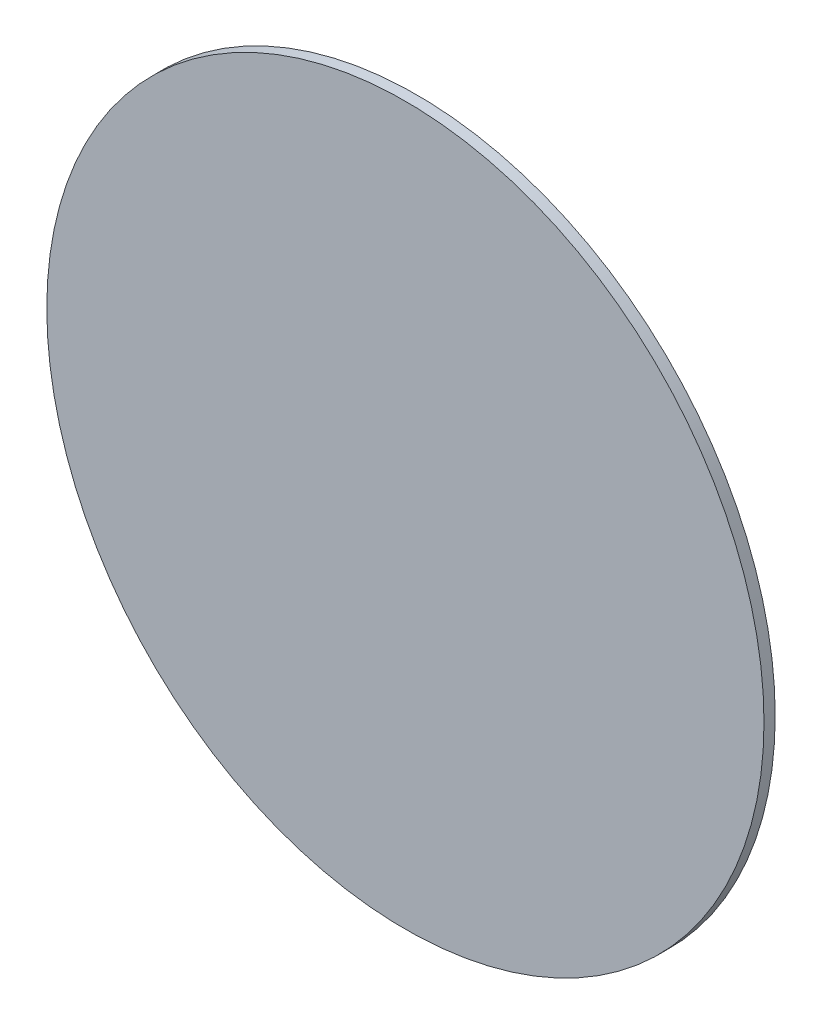
SolidWorks part; units mm, degrees
ref_plane "Front Plane" through (0, 0, 0) normal (0, 0, 1) x (1, 0, 0)
ref_plane "Top Plane" through (0, 0, 0) normal (0, 1, 0) x (1, 0, 0)
ref_plane "Right Plane" through (0, 0, 0) normal (1, 0, 0) x (0, 0, -1)
sketch "Sketch1" plane through (0, 0, 0) normal (0, 0, 1) x (1, 0, 0)
  circle A0 centre (0, -145.5758) radius 101.6
  dimension "D1" = 203.2
extrude "Boss-Extrude1" add sketch "Sketch1" along normal blind 3.175
